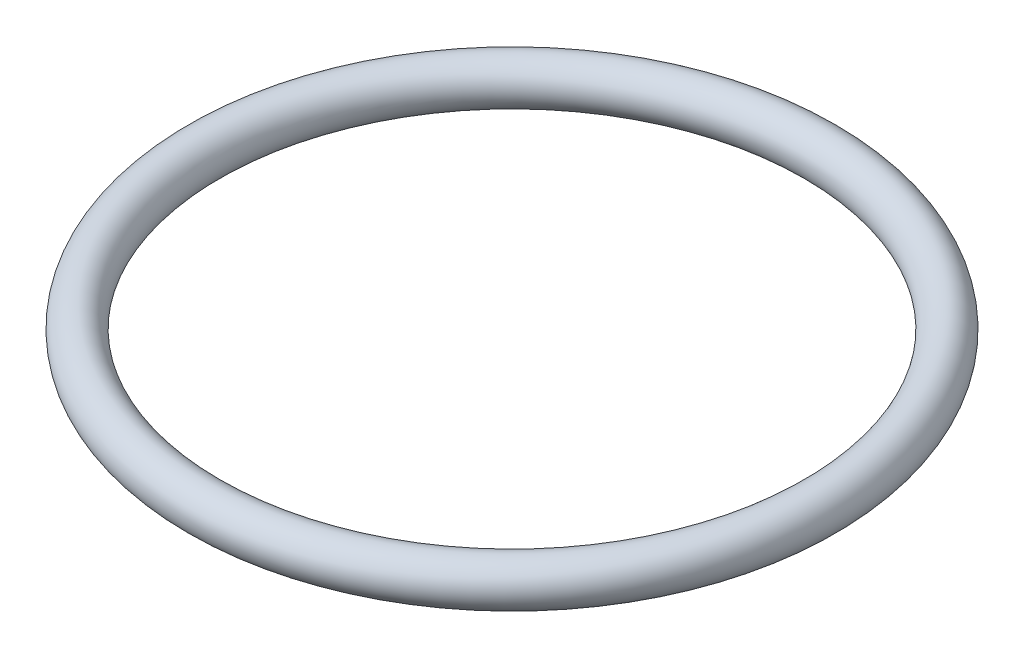
SolidWorks part; units mm, degrees
material "Oak"
ref_plane "Front Plane" through (0, 0, 0) normal (0, 0, 1) x (1, 0, 0)
ref_plane "Top Plane" through (0, 0, 0) normal (0, 1, 0) x (1, 0, 0)
ref_plane "Right Plane" through (0, 0, 0) normal (1, 0, 0) x (0, 0, -1)
sketch "Sketch2" plane through (0, 0, 0) normal (1, 0, 0) x (0, 0, -1)
  line L0 (0, 0) -> (0, 38.4939)
  circle A0 centre (175, 0) radius 12.5
  dimension "D1" = 25
  dimension "D2" = 175
revolve "Revolve1" add sketch "Sketch2" angle 360 about L0
